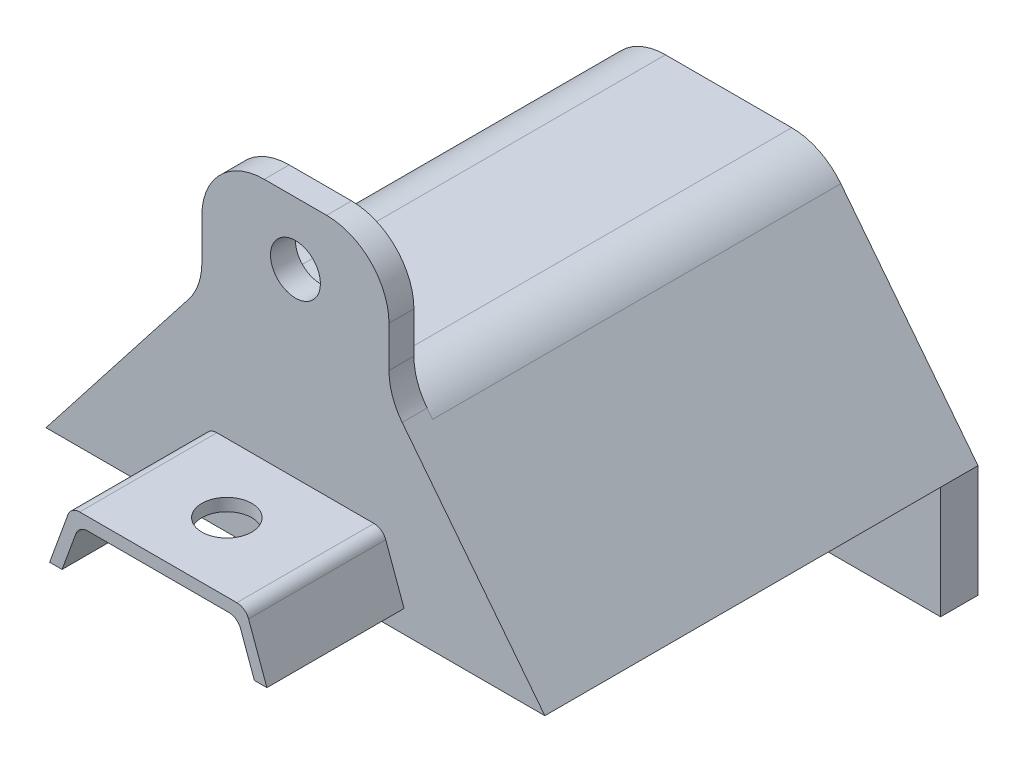
SolidWorks part; units mm, degrees
ref_plane "Front Plane" through (0, 0, 0) normal (0, 0, 1) x (1, 0, 0)
ref_plane "Top Plane" through (0, 0, 0) normal (0, 1, 0) x (1, 0, 0)
ref_plane "Right Plane" through (0, 0, 0) normal (1, 0, 0) x (0, 0, -1)
sketch "Sketch1" plane through (0, 0, 0) normal (0, 0, 1) x (1, 0, 0)
  line L1 (0, 0) -> (40, 0)
  line L2 (0, 0) -> (0, 25)
  line L3 (0, 25) -> (40, 25)
  line L4 (40, 0) -> (40, 25)
  circle A0 centre (10, 5) radius 2.5
  circle A1 centre (30, 5) radius 2.5
  dimension "D1" = 40
  dimension "D2" = 5
  dimension "D3" = 20
  dimension "D4" = 10
  dimension "D5" = 25
  dimension "D6" = 5
extrude "Boss-Extrude1" add sketch "Sketch1" along normal blind 34.73
sketch "Sketch2" plane through (0, 0, 34.73) normal (0, 0, 1) x (1, 0, 0)
  line L1 (20, 27.072) -> (20, 11.4224) construction
  line L7 (27, 15.5) -> (13, 15.5)
  line L8 (13, 15.5) -> (11.2899, 10.8015)
  line L9 (11.2899, 10.8015) -> (12.2899, 10.8015)
  line L10 (12.2899, 10.8015) -> (13.636, 14.5)
  line L11 (13.636, 14.5) -> (26.364, 14.5)
  line L12 (27.7101, 10.8015) -> (26.364, 14.5)
  line L13 (28.7101, 10.8015) -> (27.7101, 10.8015)
  line L14 (27, 15.5) -> (28.7101, 10.8015)
  line L16 (40, 25) -> (0, 25) construction
  point P4 (20, 25)
  point P11 (20, 14.5)
  point P14 (20, 15.5)
  dimension "D2" = 7
  dimension "D3" = 1
  dimension "D4" = 110
  dimension "D5" = 5
  dimension "D6" = 1
  dimension "D7" = 9.5
extrude "Boss-Extrude2" add sketch "Sketch2" along normal blind 11
fillet "Fillet3" radius 1 4 edges at (27, 15.5, 40.23) (13, 15.5, 40.23) (26.364, 14.5, 40.23) (13.636, 14.5, 40.23)
sketch "Sketch5" plane through (0, 25, 0) normal (0, 1, 0) x (1, 0, 0)
  line L0 (40, -34.73) -> (0, -34.73) construction
  line L1 (27.5, -34.73) -> (12.5, -34.73)
  line L2 (27.5, -34.73) -> (27.5, -32.73)
  line L3 (27.5, -32.73) -> (12.5, -32.73)
  line L4 (12.5, -34.73) -> (12.5, -32.73)
  line L5 (40, -34.73) -> (40, 0) construction
  dimension "D1" = 15
  dimension "D2" = 12.5
  dimension "D3" = 2
extrude "Boss-Extrude3" add sketch "Sketch5" along normal blind 10
sketch "Sketch7" plane through (0, 14.5, 0) normal (0, -1, 0) x (1, 0, 0)
  line L0 (14.3362, 45.73) -> (25.6638, 45.73) construction
  line L1 (25.6638, 34.73) -> (25.6638, 45.73) construction
  circle A0 centre (20, 40.23) radius 2
  point P5 (20, 45.73)
  point P8 (25.6638, 40.23)
  dimension "D1" = 4
sketch "Sketch8" plane through (0, 0, 34.73) normal (0, 0, 1) x (1, 0, 0)
  line L0 (12.5, 35) -> (27.5, 35) construction
  line L1 (27.5, 35) -> (27.5, 25) construction
  circle A0 centre (20, 30) radius 2
  point P4 (20, 35)
  point P7 (27.5, 30)
  dimension "D1" = 4
extrude "Cut-Extrude4" cut sketch "Sketch8" against normal through all both and the other way through all
sketch "Sketch10" plane through (0, 0, 34.73) normal (0, 0, 1) x (1, 0, 0)
  line L0 (40, 0) -> (40, 25) construction
  line L1 (0, 0) -> (40, 0)
  line L2 (0, 0) -> (0, 9)
  line L3 (0, 9) -> (40, 9)
  line L4 (40, 0) -> (40, 9)
  dimension "D1" = 9
extrude "Cut-Extrude5" cut sketch "Sketch10" against normal blind 22
sketch "Sketch12" plane through (0, 0, 34.73) normal (0, 0, 1) x (1, 0, 0)
  line L0 (12.5, 25) -> (0, 9)
  line L1 (27.5, 25) -> (40, 9)
  line L2 (0, 9) -> (0, 25)
  line L3 (0, 25) -> (12.5, 25)
  line L4 (27.5, 25) -> (40, 25)
  line L5 (40, 25) -> (40, 9)
extrude "Cut-Extrude7" cut sketch "Sketch12" against normal through all
extrude "Cut-Extrude9" cut sketch "Sketch7" against normal blind 22
sketch "Sketch14" plane through (0, 0, 0) normal (0, 0, -1) x (-1, 0, 0)
  line L0 (-40, 9) -> (0, 9) construction
  line L1 (-36.6567, 10.5) -> (-26.5, 23.5)
  line L2 (-26.5, 23.5) -> (-13.5, 23.5)
  line L3 (-13.5, 23.5) -> (-3.3433, 10.5)
  line L4 (-36.6567, 10.5) -> (-3.3433, 10.5)
  line L6 (-27.5, 25) -> (-12.5, 25) construction
  point P12 (-20, 10.5)
  point P13 (-20, 9)
  dimension "D1" = 1.5
  dimension "D2" = 1.5
  dimension "D3" = 52
  dimension "D4" = 52
  dimension "D5" = 13
extrude "Cut-Extrude8" cut sketch "Sketch14" against normal blind 22
fillet "Fillet7" radius 5 1 edges at (27.5, 25, 16.365)
fillet "Fillet8" radius 5 1 edges at (27.5, 25, 33.73)
fillet "Fillet9" radius 5 1 edges at (12.5, 25, 16.365)
fillet "Fillet10" radius 5 1 edges at (12.5, 25, 33.73)
fillet "Fillet11" radius 5 1 edges at (3.3433, 10.5, 11)
fillet "Fillet12" radius 5 1 edges at (36.6567, 10.5, 11)
fillet "Fillet13" radius 5 1 edges at (26.5, 23.5, 11)
fillet "Fillet14" radius 5 1 edges at (13.5, 23.5, 11)
fillet "Fillet15" radius 5 1 edges at (27.5, 35, 33.73)
fillet "Fillet16" radius 5 1 edges at (12.5, 35, 33.73)
sketch "Sketch15" plane through (0, 0, 12.73) normal (0, 0, 1) x (1, 0, 0)
  line L1 (0, 9) -> (40, 9)
  line L2 (0, 9) -> (0, 0)
  line L3 (0, 0) -> (40, 0)
  line L4 (40, 9) -> (40, 0)
extrude "Cut-Extrude10" cut sketch "Sketch15" against normal offset from surface (9.73 mm away) 3 up to face at (20, 18.3451, 0)
